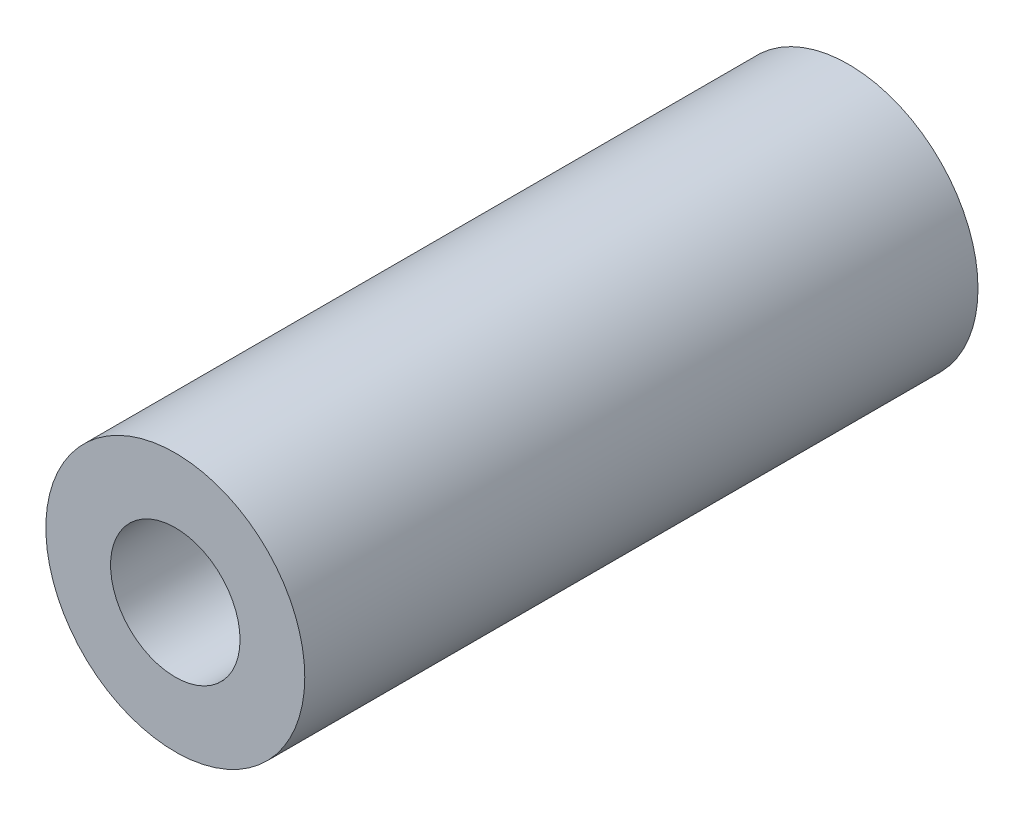
SolidWorks part; units mm, degrees
material "Plastique personnalisé"
ref_plane "Plan de face" through (0, 0, 0) normal (0, 0, 1) x (1, 0, 0)
ref_plane "Plan de dessus" through (0, 0, 0) normal (0, 1, 0) x (1, 0, 0)
ref_plane "Plan de droite" through (0, 0, 0) normal (1, 0, 0) x (0, 0, -1)
sketch "Esquisse1" plane through (0, 0, 0) normal (0, 0, 1) x (1, 0, 0)
  circle A0 centre (0, 0) radius 1.25
  circle A1 centre (0, 0) radius 2.5
extrude "Boss.-Extru.1" add sketch "Esquisse1" along normal blind 13
sketch "Esquisse2" plane through (0, 0, 0) normal (0, 1, 0) x (1, 0, 0)
  line L1 (-2.5, 0) -> (2.5, 0)
  line L2 (-2.5, 0) -> (-2.5, -13)
  line L3 (-2.5, -13) -> (2.5, -13)
  line L4 (2.5, 0) -> (2.5, -13)
